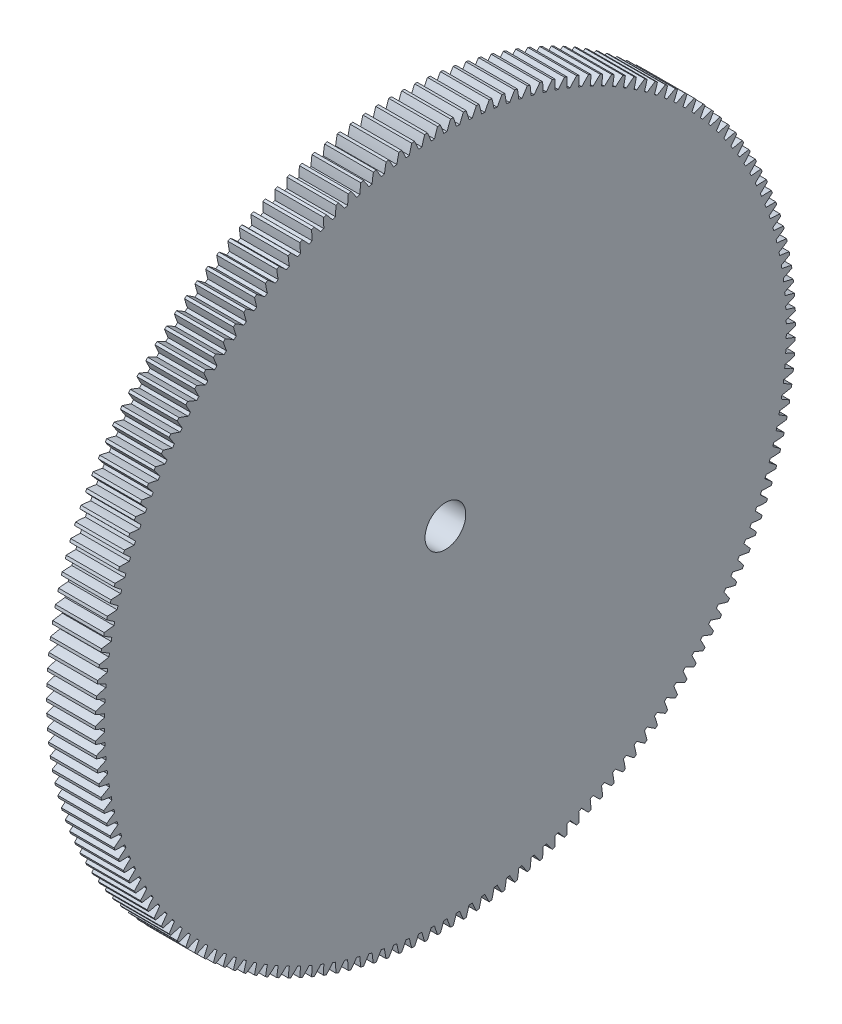
SolidWorks part; units mm, degrees
ref_plane "Plane1" through (0, 0, 0) normal (0, 0, 1) x (1, 0, 0)
ref_plane "Plane2" through (0, 0, 0) normal (0, 1, 0) x (1, 0, 0)
ref_plane "Plane3" through (0, 0, 0) normal (1, 0, 0) x (0, 0, -1)
other "Configuration Table"
sketch "HoldingSke" plane through (0, 0, 0) normal (0, 1, 0) x (1, 0, 0)
  line L0 (0, 0) -> (-0.9848, -0.1736)
  line L1 (-15, 0) -> (100, 0) construction
  line L2 (0, 0) -> (-2.1039, 2.3779)
  line L3 (0, 0) -> (-11.863, 4.5341)
  line L4 (0, 0) -> (-8.5048, 1.4996)
  line L5 (0, 0) -> (-46.8476, -17.4728)
  line L6 (0, 0) -> (-9.9476, -6.7116)
  line L7 (-2.1039, 2.3779) -> (8.6586, 51.2059)
  line L8 (-76.2, 54.61) -> (-74.4, 54.61)
  line L9 (-71.009, 38.7566) -> (-53.1078, 45.2721)
  line L10 (-76.2, 71.12) -> (104.1128, 71.12)
  line L11 (0, 0) -> (-12, 0)
  line L12 (-76.2, 101.6) -> (-76.162, 101.6)
  line L13 (24.9733, 27.94) -> (52.9518, 28.4284)
  line L14 (24.9733, 27.94) -> (24.9743, 27.94)
  line L15 (24.9733, 27.94) -> (100.4006, 29.5858)
  line L16 (-63.627, -1) -> (-12.827, -1)
  circle A0 centre (0, 0) radius 5
  circle A1 centre (0, 0) radius 37.5
  circle A2 centre (0, 0) radius 37.5
  circle A3 centre (0, 0) radius 5
  dimension "MHD" = 75
  dimension "Hub_dia" = 75
  dimension "Bore" = 10
  dimension "MBD" = 10
  dimension "Num_teeth" = 170
  dimension "Pitch" = 1
  dimension "Overall_len" = 50
  dimension "Show_teeth" = 170
  dimension "Thickness" = 12
  dimension "OAL" = 50.0001
  dimension "T_dim" = 1.8
  dimension "Ap" = 20
  dimension "H" = 19.05
  dimension "Pitch_radius" = 180.3128
  dimension "Width" = 12
  dimension "Backlash" = 0.038
  dimension "Addendum_fac" = 1
  dimension "Dedendum_fac" = 1.25
  dimension "Clearance_fac" = 0.25
  dimension "Dedendum_add" = 0.001
  dimension "Module" = 1
sketch "BasProSke" plane through (0, 0, 0) normal (0, 1, 0) x (1, 0, 0)
  line L0 (-10, 0) -> (60, 0) construction
  line L1 (0, 0) -> (0, 86)
  line L2 (0, 0) -> (12, 0)
  line L3 (12, 0) -> (12, 86)
  line L4 (12, 86) -> (0, 86)
  dimension "Thickness" = 12
  dimension "Diameter" = 172
revolve "Base-Revolve" add sketch "BasProSke" angle 360 about L0
sketch "TooCutSke" plane through (0, 0, 0) normal (1, 0, 0) x (0, 0, -1)
  line L1 (0, 0) -> (0, 107) construction
  line L2 (0, 0) -> (-0.8519, 84.9957) construction
  line L3 (0, 0) -> (-3.1413, 169.9649) construction
  line L4 (-0.8519, 84.9957) -> (-1.5707, 84.9824) construction
  arc A0 (0.4048, 83.748) -> (-0.4048, 83.748) centre (0, 0) ccw
  arc A1 (1.2591, 86.0162) -> (-1.2591, 86.0162) centre (0, 0) ccw
  circle A2 centre (0, 0) radius 85 construction
  circle A3 centre (0, 0) radius 79.8739 construction
  arc A4 (-0.4048, 83.748) -> (-1.2591, 86.0162) centre (-32.6295, 72.9051) ccw
  arc A5 (1.2591, 86.0162) -> (0.4048, 83.748) centre (32.6295, 72.9051) ccw
  dimension "Root_dia" = 167.498
  dimension "Overcut_dia" = 172.0508
  dimension "Pitch_dia" = 170
  dimension "Base_dia" = 159.7477
  dimension "Flank_rad" = 34
  dimension "Half_ang" = 1.059
  dimension "Half_CT" = 0.7189
extrude "ToothCut" cut sketch "TooCutSke" along normal through all
fillet "Breaks" [suppressed] radius 0.02
fillet "RootFillets" [suppressed] radius 0.251
pattern_circular "TeethCuts" count 170 every 2.118 about axis through (-10, 0, 0) along (1, 0, 0) of "ToothCut", "RootFillets", "Breaks"
sketch "HubNeaOneSke" plane through (0, 0, 0) normal (-1, 0, 0) x (0, 0, 1)
  circle A0 centre (0, 0) radius 37.5
  dimension "Diameter" = 75
extrude "HubNearOne" [suppressed] add sketch "HubNeaOneSke" along normal blind 38.0001
sketch "HubNeaBotSke" plane through (0, 0, 0) normal (-1, 0, 0) x (0, 0, 1)
  circle A0 centre (0, 0) radius 37.5
  dimension "Diameter" = 75
extrude "HubNearBoth" [suppressed] add sketch "HubNeaBotSke" along normal blind 19
ref_plane "FarPln" through (12, 0, 0) normal (1, 0, 0) x (0, 0, -1)
sketch "HubFarSke" plane through (12, 0, 0) normal (1, 0, 0) x (0, 0, -1)
  circle A0 centre (0, 0) radius 37.5
  dimension "Diameter" = 75
extrude "HubFar" [suppressed] add sketch "HubFarSke" along normal blind 19
sketch "BorSke" plane through (0, 0, 0) normal (1, 0, 0) x (0, 0, -1)
  circle A0 centre (0, 0) radius 5
  dimension "Diameter" = 10
extrude "Bore" cut sketch "BorSke" along normal mid plane 100.0001
sketch "KeySke" plane through (0, 0, 0) normal (1, 0, 0) x (0, 0, -1)
  line L0 (-2, 0) -> (-2, 6.8)
  line L1 (-2, 6.8) -> (2, 6.8)
  line L2 (2, 6.8) -> (2, 0)
  line L3 (0, 0) -> (0, 34) construction
  line L4 (-2, 0) -> (2, 0)
  dimension "Offset" = 6.8
  dimension "Width" = 4
extrude "Keyway" [suppressed] cut sketch "KeySke" along normal mid plane 100.0001
pattern_circular "Keyway2" [suppressed] count 2 every 90 about axis through (-10, 0, 0) along (1, 0, 0)
equation "' \"Module@HoldingSke\" = 6.35"
equation "' \"Num_teeth@HoldingSke\" = 12"
equation "' \"Ap@HoldingSke\" =  20"
equation "' \"Ap@HoldingSke\" = 20"
equation "' \"Width@HoldingSke\" = 0.5 * 25.4"
equation "' \"Hub_dia@HoldingSke\"= 1 * 25.4"
equation "' \"Hub_dia@HoldingSke\" = 1 * 25.4"
equation "' \"Overall_len@HoldingSke\" = 1.0 * 25.4"
equation "' \"Bore@HoldingSke\" = 0.75 * 25.4"
equation "' \"T_dim@HoldingSke\" = 0.1 * 25.4"
equation "' \"Width@KeySke\" = 0.25 * 25.4"
equation "' \"Show_teeth@HoldingSke\" = 13"
equation "' \"Backlash@HoldingSke\" = 0.009 * 25.4"
equation "' \"Addendum_fac@HoldingSke\" = 1.0"
equation "' \"Dedendum_fac@HoldingSke\" = 1.25"
equation "' \"Dedendum_add@HoldingSke\" = 0.00005 * 25.4"
equation "' \"Clearance_fac@HoldingSke\" = 0.25"
equation "\"Pitch@HoldingSke\" = 1 / \"Module@HoldingSke\""
equation "\"Overcut_dia@TooCutSke\" = (\"Num_teeth@HoldingSke\" + 2 * \"Addendum_fac@HoldingSke\") / \"Pitch@HoldingSke\" + 0.002 * 25.4"
equation "\"Pitch_dia@TooCutSke\" = \"Num_teeth@HoldingSke\" / \"Pitch@HoldingSke\""
equation "\"Base_dia@TooCutSke\" = \"Num_teeth@HoldingSke\" / \"Pitch@HoldingSke\" * cos((\"Ap@HoldingSke\"  * 3.14159265 / 180))"
equation "\"Root_dia@TooCutSke\" = (\"Num_teeth@HoldingSke\" + 2) / \"Pitch@HoldingSke\" - 2 * (\"Addendum_fac@HoldingSke\" + \"Dedendum_fac@HoldingSke\") / \"Pitch@HoldingSke\" - \"Dedendum_add@HoldingSke\" * 2"
equation "\"Half_ang@TooCutSke\" = 180 / \"Num_teeth@HoldingSke\""
equation "\"Half_CT@TooCutSke\" = \"Num_teeth@HoldingSke\" / \"Pitch@HoldingSke\" * sin((3.14159265 / 2 / \"Num_teeth@HoldingSke\")) / 2 - 7 * \"Backlash@HoldingSke\" / 4"
equation "\"Flank_rad@TooCutSke\" = \"Num_teeth@HoldingSke\" / \"Pitch@HoldingSke\" / 5"
equation "\"Radius@RootFillets\" = \"Clearance_fac@HoldingSke\" / \"Pitch@HoldingSke\" + \"Dedendum_add@HoldingSke\""
equation "\"Break_rad@Breaks\" = 0.02 / \"Pitch@HoldingSke\""
equation "\"Thickness@HoldingSke\" = \"Width@HoldingSke\""
equation "\"OAL@HoldingSke\" = \"Thickness@HoldingSke\""
equation "\"MHD@HoldingSke\" = (\"Num_teeth@HoldingSke\" + 2) / \"Pitch@HoldingSke\" - 2 * (\"Addendum_fac@HoldingSke\" + \"Dedendum_fac@HoldingSke\")  / \"Pitch@HoldingSke\" - \"Dedendum_add@HoldingSke\" * 2"
equation "\"MBD@HoldingSke\" = (\"Num_teeth@HoldingSke\" + 2) / \"Pitch@HoldingSke\" - 2 * (\"Addendum_fac@HoldingSke\" + \"Dedendum_fac@HoldingSke\")  / \"Pitch@HoldingSke\" - \"Dedendum_add@HoldingSke\" * 2 - 0.002 * 25.4"
equation "\"MHD@HoldingSke\" = ((sgn( \"MHD@HoldingSke\" - \"Hub_dia@HoldingSke\" )-1)*( \"MHD@HoldingSke\" - \"Hub_dia@HoldingSke\" ))/-2+ \"Hub_dia@HoldingSke\""
equation "\"MBD@HoldingSke\" = ((sgn( \"MBD@HoldingSke\" - \"Bore@HoldingSke\" )-1)*( \"MBD@HoldingSke\" - \"Bore@HoldingSke\" ))/-2+ \"Bore@HoldingSke\""
equation "\"OAL@HoldingSke\" = ((sgn( \"OAL@HoldingSke\" - \"Overall_len@HoldingSke\" )+1)*( \"OAL@HoldingSke\" - \"Overall_len@HoldingSke\" ))/2 + \"Overall_len@HoldingSke\" + 0.000002 * 25.4"
equation "\"Num_teeth@TeethCuts\" = int( \"Show_teeth@HoldingSke\" ) + 1"
equation "\"Num_teeth@TeethCuts\" = ((sgn( \"Num_teeth@TeethCuts\" - \"Num_teeth@HoldingSke\" )-1)*( \"Num_teeth@TeethCuts\" - \"Num_teeth@HoldingSke\" ))/-2+ \"Num_teeth@HoldingSke\""
equation "\"Num_teeth@TeethCuts\" = ((sgn( \"Num_teeth@TeethCuts\" - 2.0)+1)*( \"Num_teeth@TeethCuts\" - 2.0))/2 +2.0"
equation "\"Angle@TeethCuts\" = 360.0 / \"Num_teeth@HoldingSke\""
equation "\"Diameter@BasProSke\" = (\"Num_teeth@HoldingSke\" + 2 * \"Addendum_fac@HoldingSke\") / \"Pitch@HoldingSke\""
equation "\"Thickness@BasProSke\"  = \"Thickness@HoldingSke\""
equation "' \"Fillet_rad@BasProSke\" =  \"Thickness@HoldingSke\" * 0.05"
equation "' \"Fillet_rad@BasProSke\" = \"Thickness@HoldingSke\" * 0.05"
equation "\"MHD@HoldingSke\" = ((sgn( \"MHD@HoldingSke\" - \"Root_dia@TooCutSke\" )-1)*( \"MHD@HoldingSke\" - \"Root_dia@TooCutSke\" ))/-2+ \"Root_dia@TooCutSke\""
equation "\"Diameter@HubNeaOneSke\" = \"MHD@HoldingSke\""
equation "\"Length@HubNearOne\" = \"OAL@HoldingSke\" - \"Thickness@BasProSke\""
equation "\"Diameter@HubNeaBotSke\" = \"MHD@HoldingSke\""
equation "\"Length@HubNearBoth\" = ( \"OAL@HoldingSke\" - \"Thickness@BasProSke\" ) / 2.0"
equation "\"Thickness@FarPln\" = \"Thickness@BasProSke\""
equation "\"Diameter@HubFarSke\" = \"MHD@HoldingSke\""
equation "\"Length@HubFar\" = ( \"OAL@HoldingSke\" - \"Thickness@BasProSke\" ) / 2.0"
equation "\"Diameter@BorSke\" = \"MBD@HoldingSke\""
equation "\"D1@Bore\" = \"OAL@HoldingSke\" * 2.0"
equation "\"D1@Keyway\" = \"OAL@HoldingSke\" * 2.0"
equation "\"Offset@KeySke\" = \"T_dim@HoldingSke\" + \"MBD@HoldingSke\" / 2.0"
